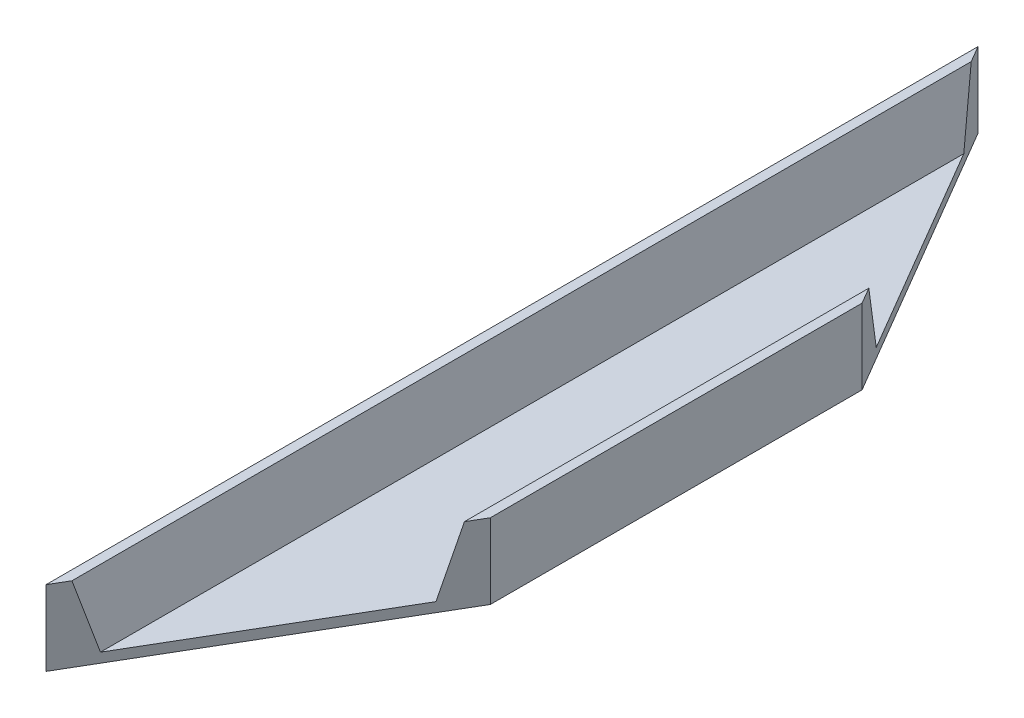
SolidWorks part; units mm, degrees
ref_plane "Front Plane" through (0, 0, 0) normal (0, 0, 1) x (1, 0, 0)
ref_plane "Top Plane" through (0, 0, 0) normal (0, 1, 0) x (1, 0, 0)
ref_plane "Right Plane" through (0, 0, 0) normal (1, 0, 0) x (0, 0, -1)
sketch "Sketch1" plane through (0, 0, 0) normal (0, 0, 1) x (1, 0, 0)
  line L0 (-28.7655, -12.9858) -> (28.7655, -12.9858)
  line L1 (38.1, 17.4308) -> (-38.1, 17.4307) construction
  line L2 (38.1, 17.4308) -> (38.1, -17.4307)
  line L3 (38.1, -17.4307) -> (-38.1, -17.4308)
  line L4 (-38.1, 17.4307) -> (-38.1, -17.4308)
  line L5 (38.1, 17.4308) -> (-38.1, -17.4308) construction
  line L6 (38.1, -17.4307) -> (-38.1, 17.4307) construction
  line L7 (28.7655, -12.9858) -> (33.655, 17.4308)
  line L8 (-33.655, 17.4307) -> (-28.7655, -12.9858)
  line L9 (-38.1, 17.4307) -> (-33.655, 17.4307)
  line L10 (33.655, 17.4308) -> (38.1, 17.4308)
  point P0 (0, 0)
  dimension "D1" = 34.8615
  dimension "D2" = 76.2
  dimension "D3" = 4.445
  dimension "D4" = 9.3345
  dimension "D5" = 9.3345
  dimension "D6" = 4.445
  dimension "D7" = 4.445
extrude "Boss-Extrude1" add sketch "Sketch1" along normal blind 432.4604
sketch "Sketch2" plane through (0, 0, 0) normal (0, 1, 0) x (1, 0, 0)
  line L0 (-38.1, 0) -> (38.1, -129.9972)
  line L2 (38.1, -432.4604) -> (38.1, 0) construction
  line L3 (-38.1, -432.4604) -> (38.1, -302.4632)
  line L4 (38.1, -129.9972) -> (38.1, 0)
  line L5 (38.1, 0) -> (-38.1, 0)
  line L6 (38.1, -302.4632) -> (38.1, -432.4604)
  line L7 (38.1, -432.4604) -> (-38.1, -432.4604)
  dimension "D1" = 172.466
extrude "Cut-Extrude1" cut sketch "Sketch2" against normal through all and the other way through all
